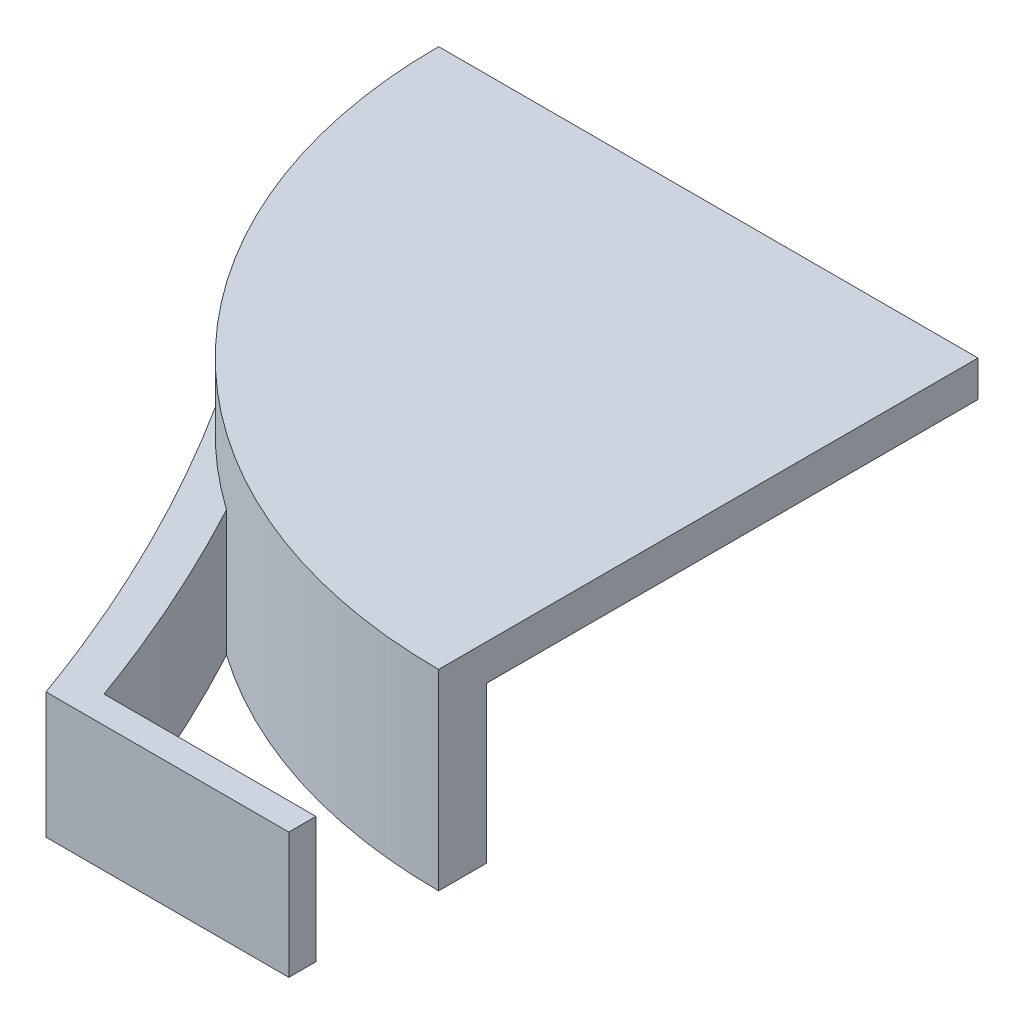
SolidWorks part; units mm, degrees
ref_plane "Front Plane" through (0, 0, 0) normal (0, 0, 1) x (1, 0, 0)
ref_plane "Top Plane" through (0, 0, 0) normal (0, 1, 0) x (1, 0, 0)
ref_plane "Right Plane" through (0, 0, 0) normal (1, 0, 0) x (0, 0, -1)
sketch "Sketch1" plane through (0, 0, 0) normal (0, 1, 0) x (1, 0, 0)
  circle A0 centre (0, 0) radius 18
  circle A1 centre (0, 0) radius 16.4
extrude "Boss-Extrude1" add sketch "Sketch1" along normal blind 6.4
sketch "Sketch2" plane through (0, 6.4, 0) normal (0, 1, 0) x (1, 0, 0)
  circle A0 centre (0, 0) radius 16.4
extrude "Boss-Extrude2" add sketch "Sketch2" against normal blind 1.2
sketch "Sketch3" plane through (0, 6.4, 0) normal (0, 1, 0) x (1, 0, 0)
  line L1 (0, 0) -> (-28.9449, 0)
  line L2 (0, 0) -> (0, 19.3729)
  line L3 (0, 19.3729) -> (-28.9449, 19.3729)
  line L4 (-28.9449, 0) -> (-28.9449, 19.3729)
  line L5 (0, 0) -> (25.8306, 0)
  line L6 (0, 0) -> (0, 19.3729)
  line L7 (0, 19.3729) -> (25.8306, 19.3729)
  line L8 (25.8306, 0) -> (25.8306, 19.3729)
  circle M5 centre (0, 0) radius 18
extrude "Cut-Extrude1" cut sketch "Sketch3" against normal blind 9.2 contours L2 L5 M5 | L1 L2 M5 | L5 L8 L7 L2 M5 | L4 L1 L2 L3 M5
sketch "Sketch4" plane through (0, 6.4, 0) normal (0, 1, 0) x (1, 0, 0)
  line L1 (0, 0) -> (21.7295, 0)
  line L2 (0, 0) -> (0, -20.9618)
  line L3 (0, -20.9618) -> (21.7295, -20.9618)
  line L4 (21.7295, 0) -> (21.7295, -20.9618)
extrude "Cut-Extrude2" cut sketch "Sketch4" against normal blind 9.2
sketch "Sketch7" plane through (0, 0, 0) normal (0, -1, 0) x (1, 0, 0)
  line L0 (0, 22.0949) -> (0, 23)
  line L1 (0, 23) -> (-8.1027, 23)
  line L2 (-7.0715, 22.0949) -> (0, 22.0949)
  arc A1 (-10.3537, 14.7241) -> (-13.6085, 11.7817) centre (0, 0) ccw
  spline S0 degree 3 poles (-13.6085, 11.7817) (-11.3441, 15.3336) (-9.5088, 19.073) (-8.1027, 23) knots 0.222402 0.222402 0.222402 0.222402 0.927766 0.927766 0.927766 0.927766
  spline S1 degree 3 poles (-10.3537, 14.7241) (-9.0588, 17.1432) (-7.9492, 19.6432) (-7.025, 22.2242) knots 0.464158 0.464158 0.464158 0.464158 0.927766 0.927766 0.927766 0.927766
extrude "Boss-Extrude3" add sketch "Sketch7" against normal blind 4.2
